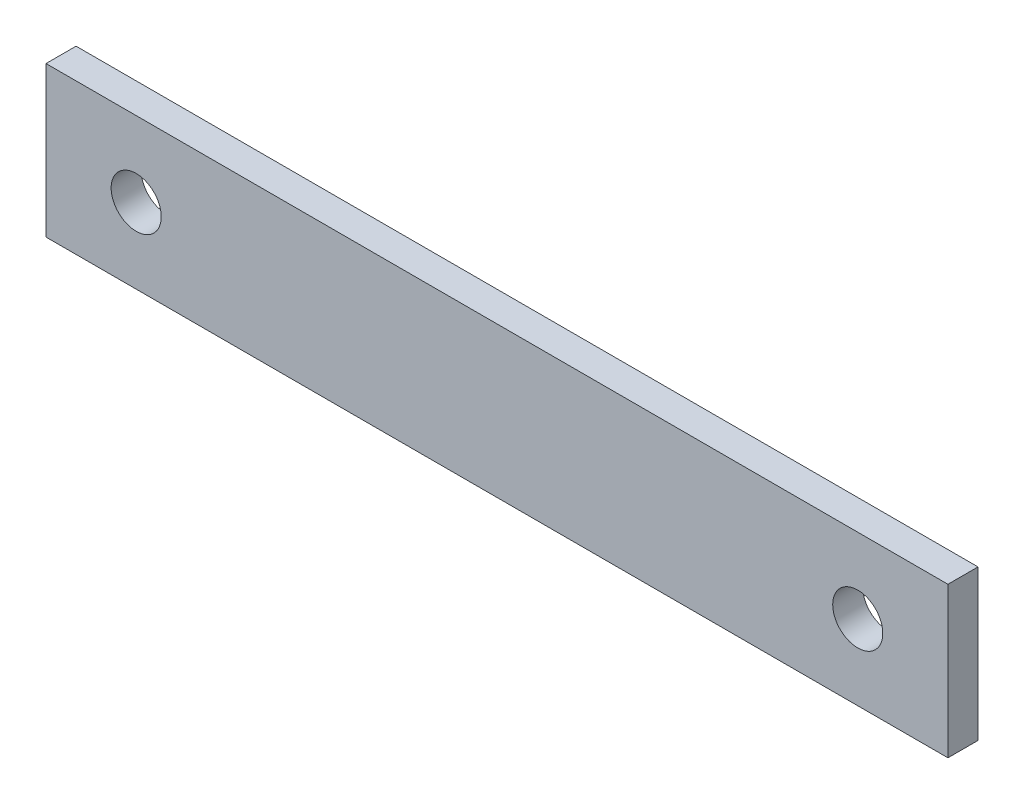
SolidWorks part; units mm, degrees
ref_plane "Front Plane" through (0, 0, 0) normal (0, 0, 1) x (1, 0, 0)
ref_plane "Top Plane" through (0, 0, 0) normal (0, 1, 0) x (1, 0, 0)
ref_plane "Right Plane" through (0, 0, 0) normal (1, 0, 0) x (0, 0, -1)
sketch "Sketch1" plane through (0, 0, 0) normal (0, 0, 1) x (1, 0, 0)
  line L0 (0, 0) -> (90, 0)
  line L1 (90, 0) -> (90, 15)
  line L2 (90, 15) -> (0, 15)
  line L3 (0, 15) -> (0, 0)
  line L4 (0, 7.5) -> (90, 7.5) construction
  line L5 (45, 15) -> (45, 0) construction
  line L6 (45, 7.5) -> (25, 7.5) construction
  line L7 (45, 7.5) -> (9, 7.5) construction
  circle A1 centre (9, 7.5) radius 2.5
  circle A3 centre (81, 7.5) radius 2.5
extrude "Boss-Extrude1" add sketch "Sketch1" along normal blind 3
